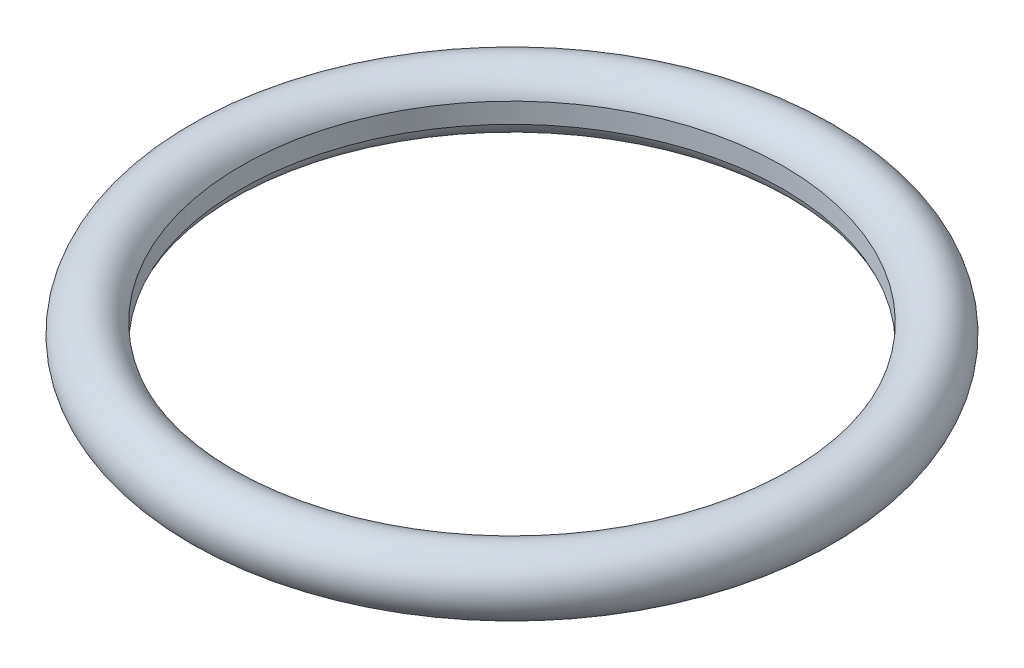
SolidWorks part; units mm, degrees
ref_plane "Front Plane" through (0, 0, 0) normal (0, 0, 1) x (1, 0, 0)
ref_plane "Top Plane" through (0, 0, 0) normal (0, 1, 0) x (1, 0, 0)
ref_plane "Right Plane" through (0, 0, 0) normal (1, 0, 0) x (0, 0, -1)
sketch "Sketch2" plane through (0, 0, 0) normal (0, 0, 1) x (1, 0, 0)
  line L0 (0, 0) -> (-13.5, 0) construction
  line L1 (-13.5, -0.5) -> (-13.5, 0.5)
  line L2 (0, 0) -> (0, 4.834) construction
  arc A0 (-13.5, 0.5) -> (-13.5, -0.5) centre (-14.9142, 0) ccw
  point P4 (-13.5, 0)
  dimension "D1" = 3
  dimension "D2" = 13.5
  dimension "D3" = 1
revolve "Revolve1" add sketch "Sketch2" angle 360 about L2
